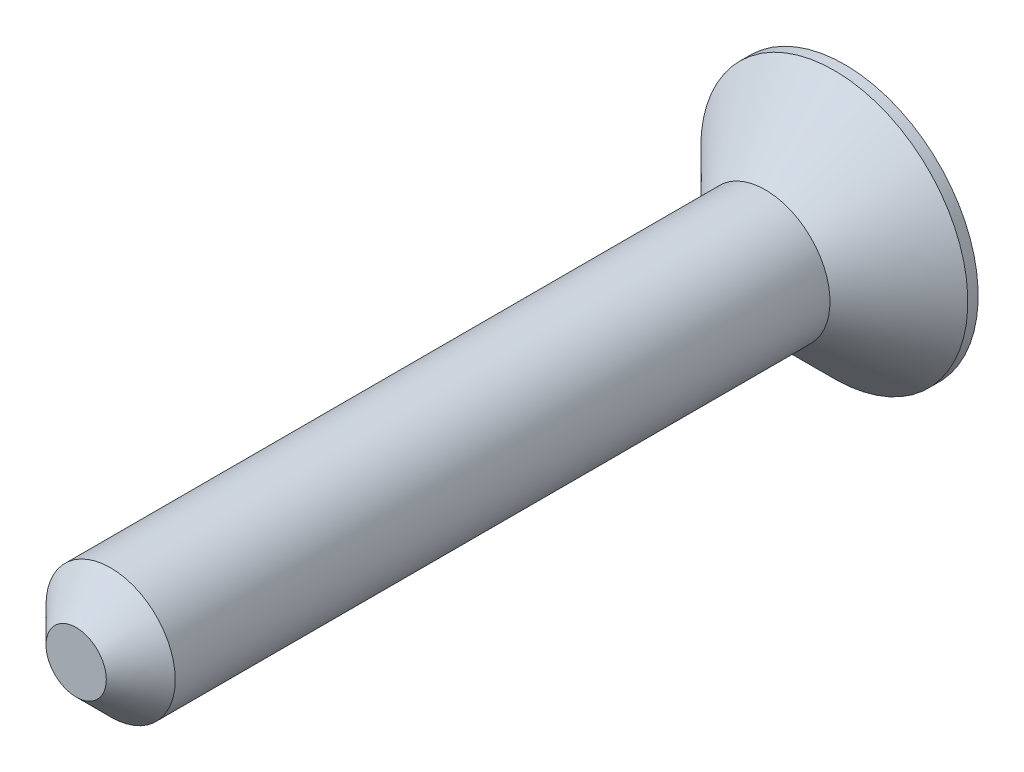
SolidWorks part; units mm, degrees
ref_plane "Front" through (0, 0, 0) normal (0, 0, 1) x (1, 0, 0)
ref_plane "Top" through (0, 0, 0) normal (0, 1, 0) x (1, 0, 0)
ref_plane "Right" through (0, 0, 0) normal (1, 0, 0) x (0, 0, -1)
sketch "Sketch1" plane through (0, 0, 0) normal (0, 0, 1) x (1, 0, 0)
  circle A0 centre (0, 0) radius 4.7625
  dimension "D1" = 9.525
extrude "Base-Extrude" add sketch "Sketch1" along normal blind 50.8
sketch "Sketch2" plane through (0, 0, 0) normal (0, 0, -1) x (-1, 0, 0)
  circle A1 centre (0, 0) radius 4.7625
  circle A2 centre (0, 0) radius 4.7625
  dimension "D1" = 0
extrude "Boss-Extrude1" add sketch "Sketch2" along normal blind 5.08 draft 45
sketch "Sketch3" plane through (0, 0, -5.08) normal (0, 0, -1) x (-1, 0, 0)
  line L0 (0, 0) -> (0, 3.2691) construction
  line L1 (-0.8771, 4.2259) -> (-0.8771, 0)
  line L2 (0.8771, 4.2259) -> (0.8771, 0)
  line L3 (-0.8771, 4.2259) -> (0.8771, 4.2259)
  line L4 (-0.8771, 0) -> (0.8771, 0)
extrude "Cut-Extrude1" cut sketch "Sketch3" against normal blind 3.175
pattern_circular "CirPattern1" count 4 over 360
sketch "Sketch4" plane through (0, 0, -5.08) normal (0, 0, -1) x (-1, 0, 0)
  line L12 (-0.8771, 0.8771) -> (-4.2259, 0.8771)
  line L13 (-0.8771, 4.2259) -> (-0.8771, 0.8771)
  line L14 (0.8771, 4.2259) -> (-0.8771, 4.2259)
  line L15 (0.8771, 0.8771) -> (0.8771, 4.2259)
  line L16 (4.2259, 0.8771) -> (0.8771, 0.8771)
  line L17 (4.2259, -0.8771) -> (4.2259, 0.8771)
  line L18 (0.8771, -0.8771) -> (4.2259, -0.8771)
  line L19 (0.8771, -4.2259) -> (0.8771, -0.8771)
  line L20 (-0.8771, -4.2259) -> (0.8771, -4.2259)
  line L21 (-0.8771, -0.8771) -> (-0.8771, -4.2259)
  line L22 (-4.2259, -0.8771) -> (-0.8771, -0.8771)
  line L23 (-4.2259, 0.8771) -> (-4.2259, -0.8771)
  line L24 (-0.8771, 0.8771) -> (-4.2259, 0.8771)
  line L25 (-0.8771, 4.2259) -> (-0.8771, 0.8771)
  line L26 (0.8771, 4.2259) -> (-0.8771, 4.2259)
  line L27 (0.8771, 0.8771) -> (0.8771, 4.2259)
  line L28 (4.2259, 0.8771) -> (0.8771, 0.8771)
  line L29 (4.2259, -0.8771) -> (4.2259, 0.8771)
  line L30 (0.8771, -0.8771) -> (4.2259, -0.8771)
  line L31 (0.8771, -4.2259) -> (0.8771, -0.8771)
  line L32 (-0.8771, -4.2259) -> (0.8771, -4.2259)
  line L33 (-0.8771, -0.8771) -> (-0.8771, -4.2259)
  line L34 (-4.2259, -0.8771) -> (-0.8771, -0.8771)
  line L35 (-4.2259, 0.8771) -> (-4.2259, -0.8771)
  circle A1 centre (0, 0) radius 9.8425
  circle A2 centre (0, 0) radius 9.8425
  dimension "D1" = 0
  dimension "D2" = 0
extrude "Boss-Extrude2" add sketch "Sketch4" along normal blind 0.762
chamfer "Chamfer1" distance 2.54 angle 45
